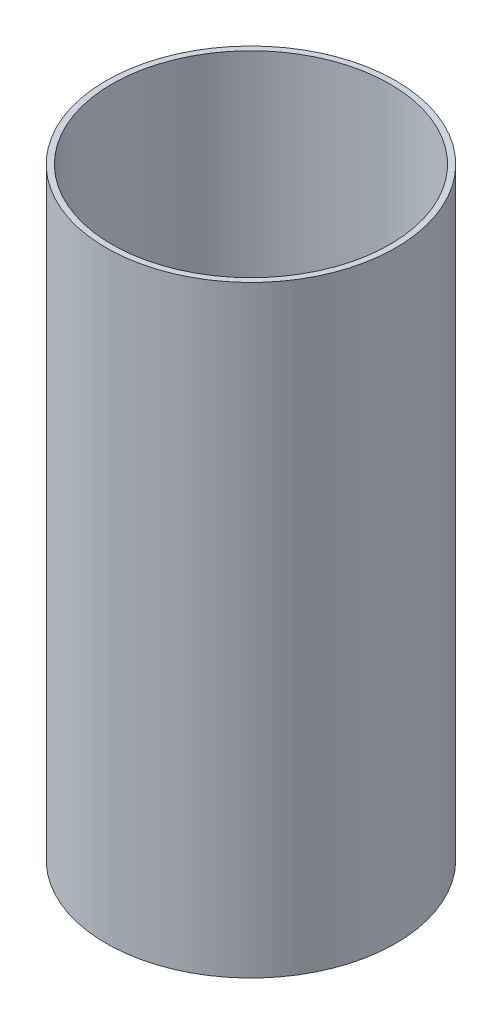
SolidWorks part; units mm, degrees
ref_plane "Front" through (0, 0, 0) normal (0, 0, 1) x (1, 0, 0)
ref_plane "Top" through (0, 0, 0) normal (0, 1, 0) x (1, 0, 0)
ref_plane "Right" through (0, 0, 0) normal (1, 0, 0) x (0, 0, -1)
imported_body "40560-40040-1/40560-40040-1-surface1"
imported_body "40560-40040-1/40560-40040-1-surface2"
imported_body "40560-40040-1/40560-40040-1-surface3"
imported_body "40560-40040-1/40560-40350-1-surface1"
imported_body "40560-40040-1/56000-00770-1-surface1"
imported_body "quill-1-surface1"
sketch "Sketch1" plane through (0, 0, 0) normal (0, -1, 0) x (1, 0, 0)
  circle A0 centre (0, 24.9999) radius 3
  circle A1 centre (0, 24.9999) radius 3.125 construction
  circle A2 centre (0, 24.9999) radius 3.125
  dimension "D1" = 6
extrude "Extrude1" add sketch "Sketch1" against normal blind 13
